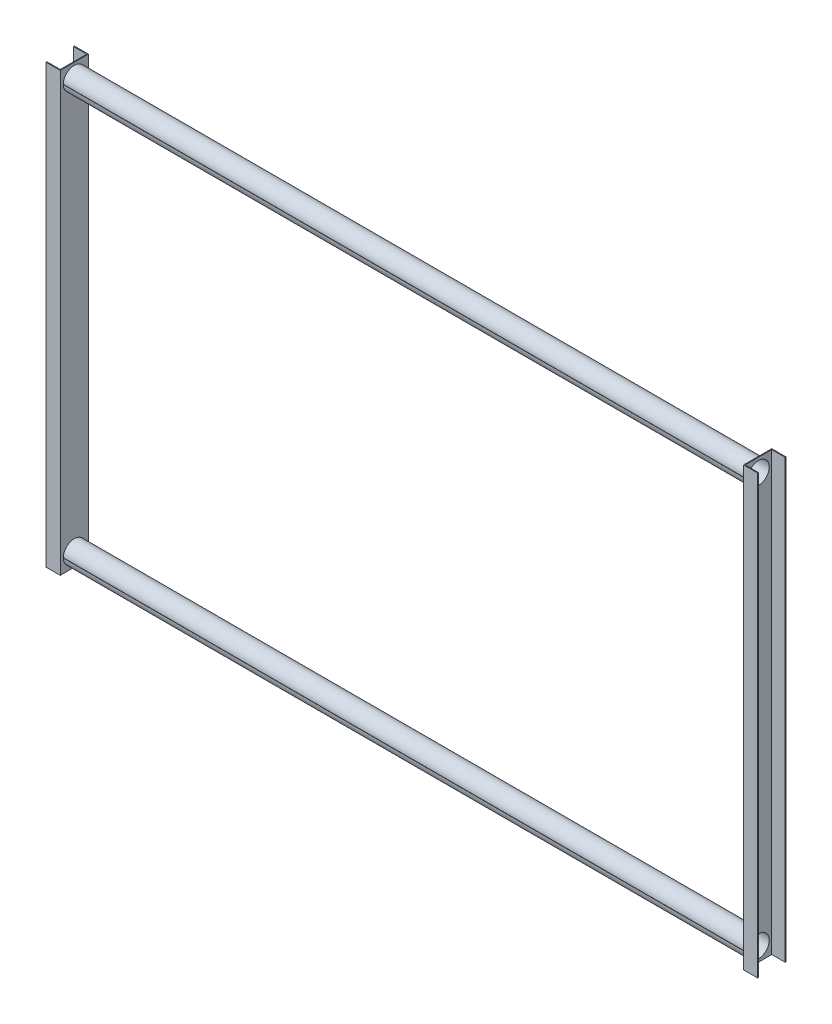
SolidWorks part; units mm, degrees
ref_plane "Front Plane" through (0, 0, 0) normal (0, 0, 1) x (1, 0, 0)
ref_plane "Top Plane" through (0, 0, 0) normal (0, 1, 0) x (1, 0, 0)
ref_plane "Right Plane" through (0, 0, 0) normal (1, 0, 0) x (0, 0, -1)
sketch "Sketch3" plane through (0, 0, 0) normal (0, 1, 0) x (1, 0, 0)
  line L0 (0, 209.8812) -> (0, -209.8812) construction
  line L1 (-51.5, 51.5) -> (0, 51.5)
  line L2 (-209.8812, 0) -> (209.8812, 0) construction
  line L3 (0, 51.5) -> (0, -51.5)
  line L4 (0, -51.5) -> (-51.5, -51.5)
  line L5 (-51.5, -51.5) -> (-51.5, -48.5)
  line L6 (-51.5, -48.5) -> (-3, -48.5)
  line L7 (-3, -48.5) -> (-3, 48.5)
  line L8 (-3, 48.5) -> (-51.5, 48.5)
  line L9 (-51.5, 48.5) -> (-51.5, 51.5)
  line L10 (2500, 209.8812) -> (2500, -209.8812) construction
  line L11 (1250, 209.8812) -> (1250, -209.8812) construction
  line L12 (2503, 48.5) -> (2551.5, 48.5)
  line L13 (2503, -48.5) -> (2503, 48.5)
  line L14 (2551.5, -48.5) -> (2503, -48.5)
  line L15 (2551.5, -51.5) -> (2551.5, -48.5)
  line L16 (2500, -51.5) -> (2551.5, -51.5)
  line L17 (2500, 51.5) -> (2500, -51.5)
  line L18 (2551.5, 51.5) -> (2500, 51.5)
  line L19 (2551.5, 48.5) -> (2551.5, 51.5)
  point P3 (0, 0)
  point P6 (0, 0)
  point P15 (0, 0)
  dimension "D1" = 103
  dimension "D2" = 3
  dimension "D3" = 3
  dimension "D4" = 3
  dimension "D5" = 51.5
  dimension "D6" = 51.5
  dimension "D7" = 2500
  dimension "D8" = 1250
extrude "Boss-Extrude1" add sketch "Sketch3" along normal blind 1600
sketch "Sketch4" plane through (0, 0, 0) normal (1, 0, 0) x (0, 0, -1)
  line L0 (0, 0) -> (0, 1600) construction
  line L1 (-51.5, 1600) -> (51.5, 1600) construction
  line L2 (501.2112, 800) -> (-501.2112, 800) construction
  circle A0 centre (0, 1550) radius 39.5
  circle A1 centre (0, 50) radius 39.5
  point P7 (0, 800)
  point P8 (0, 800)
  dimension "D1" = 79
  dimension "D2" = 1500
extrude "Cut-Extrude2" cut sketch "Sketch4" against normal through all and the other way through all
sketch "Sketch5" plane through (0, 0, 0) normal (1, 0, 0) x (0, 0, -1)
  line L0 (0, 50) -> (-57.3914, 50) construction
  line L1 (-39.4968, 49.5) -> (-40.4969, 49.5)
  line L2 (-39.4968, 50.5) -> (-40.4969, 50.5)
  line L3 (0, 1550) -> (-55.0176, 1550) construction
  line L4 (-39.4968, 1549.5) -> (-40.4969, 1549.5)
  line L5 (-39.4968, 1550.5) -> (-40.4969, 1550.5)
  arc A0 (-40.4969, 49.5) -> (-40.4969, 50.5) centre (0, 50) ccw
  arc A1 (-39.4968, 49.5) -> (-39.4968, 50.5) centre (0, 50) ccw
  arc A2 (-40.4969, 1549.5) -> (-40.4969, 1550.5) centre (0, 1550) ccw
  arc A3 (-39.4968, 1549.5) -> (-39.4968, 1550.5) centre (0, 1550) ccw
  circle A5 centre (0, 50) radius 40.5 construction
  circle A6 centre (0, 50) radius 39.5 construction
  circle A7 centre (0, 1550) radius 40.5 construction
  circle A8 centre (0, 1550) radius 39.5 construction
  point P15 (38.7303, 61.8411)
  point P17 (39.5, 50)
  point P22 (38.7303, 1561.8411)
  point P24 (39.5, 1550)
  dimension "D1" = 81
  dimension "D3" = 81
  dimension "D5" = 1
  dimension "D6" = 0.5
  dimension "D7" = 1
  dimension "D8" = 0.5
  dimension "D2" = 1
  dimension "D4" = 1
extrude "Boss-Extrude2" add sketch "Sketch5" along normal blind 2500
